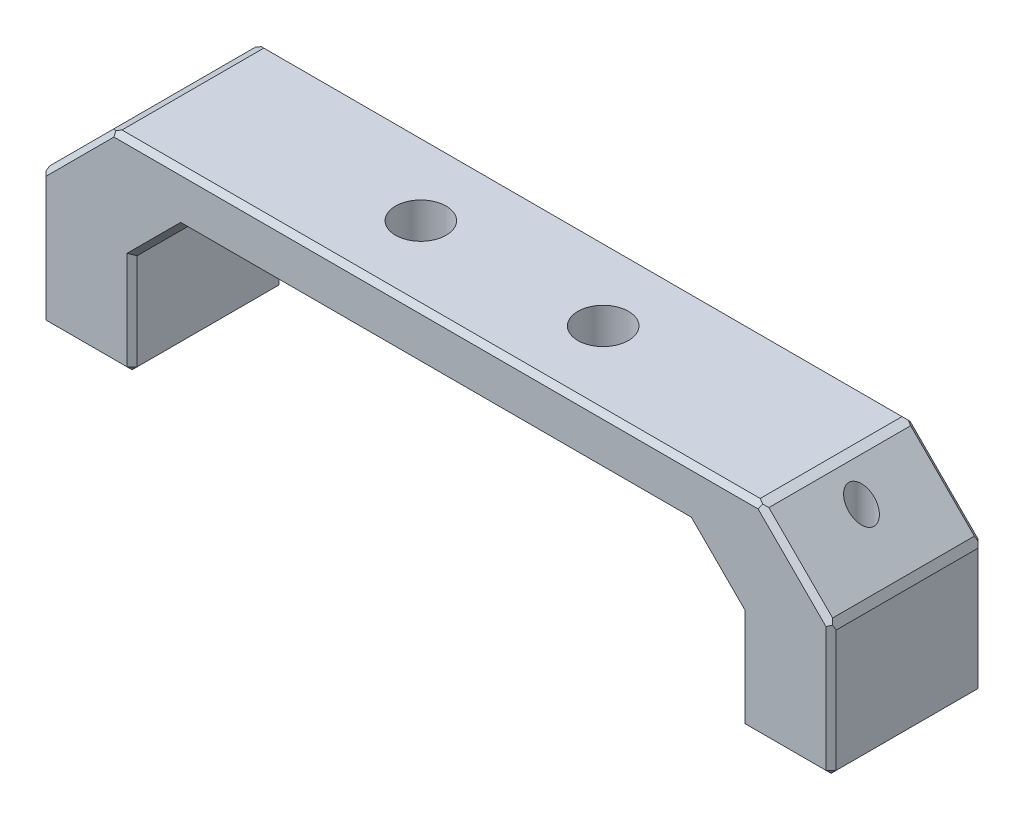
SolidWorks part; units mm, degrees
ref_plane "Plan de face" through (0, 0, 0) normal (0, 0, 1) x (1, 0, 0)
ref_plane "Plan de dessus" through (0, 0, 0) normal (0, 1, 0) x (1, 0, 0)
ref_plane "Plan de droite" through (0, 0, 0) normal (1, 0, 0) x (0, 0, -1)
sketch "Esquisse1" plane through (0, 0, 0) normal (0, 0, 1) x (1, 0, 0)
  line L0 (-39, 25.3548) -> (-39, -34.7313) construction
  line L1 (39, 49.4658) -> (39, -27.2684) construction
  line L2 (-32, 58.3983) -> (-32, -31.6829) construction
  line L3 (32, 48.4404) -> (32, -26.6273) construction
  line L4 (-39, 0) -> (39, 0) construction
  line L5 (-30, 63.1475) -> (-30, -27.3933) construction
  line L6 (30, 71.1138) -> (30, -35.9724) construction
  line L7 (-30, 0) -> (-39, 0)
  line L8 (39, 0) -> (30, 0)
  line L9 (-48.922, 15) -> (52.661, 15) construction
  line L10 (-48.922, 20) -> (52.661, 20) construction
  line L11 (-48.922, 30) -> (52.661, 30) construction
  line L17 (-30, 0) -> (-30, 15)
  line L18 (-30, 15) -> (30, 15)
  line L19 (30, 15) -> (30, 0)
  line L20 (-39, 0) -> (-39, 20)
  line L21 (-39, 20) -> (39, 20)
  line L22 (39, 20) -> (39, 0)
  dimension "D1" = 39
  dimension "D2" = 39
  dimension "D3" = 32
  dimension "D4" = 32
  dimension "D5" = 30
  dimension "D6" = 30
  dimension "D7" = 15
  dimension "D8" = 5
  dimension "D9" = 10
extrude "Boss.-Extru.1" add sketch "Esquisse1" along normal blind 15
chamfer "Chanfrein1" distance 5 angle 45 2 edges at (-30, 15, 7.5) (30, 15, 7.5)
chamfer "Chanfrein2" distance 7 angle 45 2 edges at (39, 20, 7.5) (-39, 20, 7.5)
sketch "Esquisse2" plane through (0, 20, 0) normal (0, 1, 0) x (1, 0, 0)
  line L0 (56.8198, -7.5) -> (-52.3275, -7.5) construction
  line L1 (32, -15) -> (-32, -15) construction
  line L2 (9, -21.8659) -> (9, 10.8284) construction
  line L3 (-9, -21.8659) -> (-9, 10.8284) construction
  dimension "D1" = 7.5
  dimension "D2" = 9
  dimension "D3" = 9
hole_wizard "Trou taraudé M6x1.01" positions "Esquisse3" profile "Esquisse4" tap size "M6x1.0" standard "Ansi Metric" end condition through all
sketch "Esquisse3" plane through (0, 20, 0) normal (0, 1, 0) x (1, 0, 0)
  line L0 (56.8198, -7.5) -> (-52.3275, -7.5) construction
  line L1 (9, -21.8659) -> (9, 10.8284) construction
  line L2 (-9, -21.8659) -> (-9, 10.8284) construction
  point P0 (9, -7.5)
  point P6 (-9, -7.5)
sketch "Esquisse4" plane through (9, 20, 7.5) normal (1, 0, 0) x (0, 0, 1)
  line L0 (0, 0) -> (0, 20)
  line L1 (0, 20) -> (2.5, 20)
  line L2 (2.5, 20) -> (2.5, 0)
  line L5 (2.5, 0) -> (0, 0)
  line L11 (0, -6.35) -> (0, 107.95) construction
  dimension "Diamètre du trou pour taraudage jusqu'au prochain" = 5
  dimension "Profondeur du trou pour taraudage jusqu'au prochain" = 20
cosmetic thread "Filetage de perçage1" parameters "D2"=6
cosmetic thread "Filetage de perçage2" parameters "D2"=6
sketch "Esquisse5" plane through (0, 0, 0) normal (0, -1, 0) x (-1, 0, 0)
  line L0 (-47.4313, -7.5) -> (51.2101, -7.5) construction
  line L1 (-30, 0) -> (-39, 0) construction
  line L2 (-34.5, 10.3542) -> (-34.5, -24.852) construction
  line L3 (34.5, 10.3542) -> (34.5, -24.852) construction
  dimension "D1" = 7.5
  dimension "D2" = 34.5
  dimension "D3" = 34.5
hole_wizard "Trou taraudé M3x0.51" positions "Esquisse8" profile "Esquisse9" tap size "M3x0.5" standard "Ansi Metric" end condition through all
sketch "Esquisse8" plane through (0, 0, 0) normal (0, -1, 0) x (-1, 0, 0)
  line L0 (-47.4313, -7.5) -> (51.2101, -7.5) construction
  line L1 (-34.5, 10.3542) -> (-34.5, -24.852) construction
  line L2 (34.5, 10.3542) -> (34.5, -24.852) construction
  point P0 (-34.5, -7.5)
  point P6 (34.5, -7.5)
sketch "Esquisse9" plane through (34.5, 0, 7.5) normal (1, 0, 0) x (0, 0, -1)
  line L0 (0, 0) -> (0, 20)
  line L1 (0, 20) -> (1.25, 20)
  line L2 (1.25, 20) -> (1.25, 0)
  line L5 (1.25, 0) -> (0, 0)
  line L11 (0, -6.35) -> (0, 107.95) construction
  dimension "Diamètre du trou pour taraudage jusqu'au prochain" = 2.5
  dimension "Profondeur du trou pour taraudage jusqu'au prochain" = 20
cosmetic thread "Filetage de perçage5" parameters "D2"=3
cosmetic thread "Filetage de perçage6" parameters "D2"=3
chamfer "Chanfrein6" distance 0.5 angle 45 28 edges at (39, 6.5, 15) (35.5, 16.5, 15) (0, 20, 15) (30, 5, 15) (27.5, 12.5, 15) (0, 15, 15) (-27.5, 12.5, 15) (-35.5, 16.5, 15) (-34.5, 0, 15) (-30, 5, 15) (-39, 6.5, 15) (-39, 0, 7.5) (-30, 0, 7.5) (34.5, 0, 15) (30, 0, 7.5) (39, 0, 7.5) (34.5, 0, 0) (30, 5, 0) (39, 6.5, 0) (35.5, 16.5, 0) (27.5, 12.5, 0) (0, 20, 0) (-35.5, 16.5, 0) (-39, 6.5, 0) (-34.5, 0, 0) (-30, 5, 0) (-27.5, 12.5, 0) (0, 15, 0)
chamfer "Chanfrein10" distance 0.5 angle 22.5 4 edges at (-39, 13, 7.5) (39, 13, 7.5) (32, 20, 7.5) (-32, 20, 7.5)
